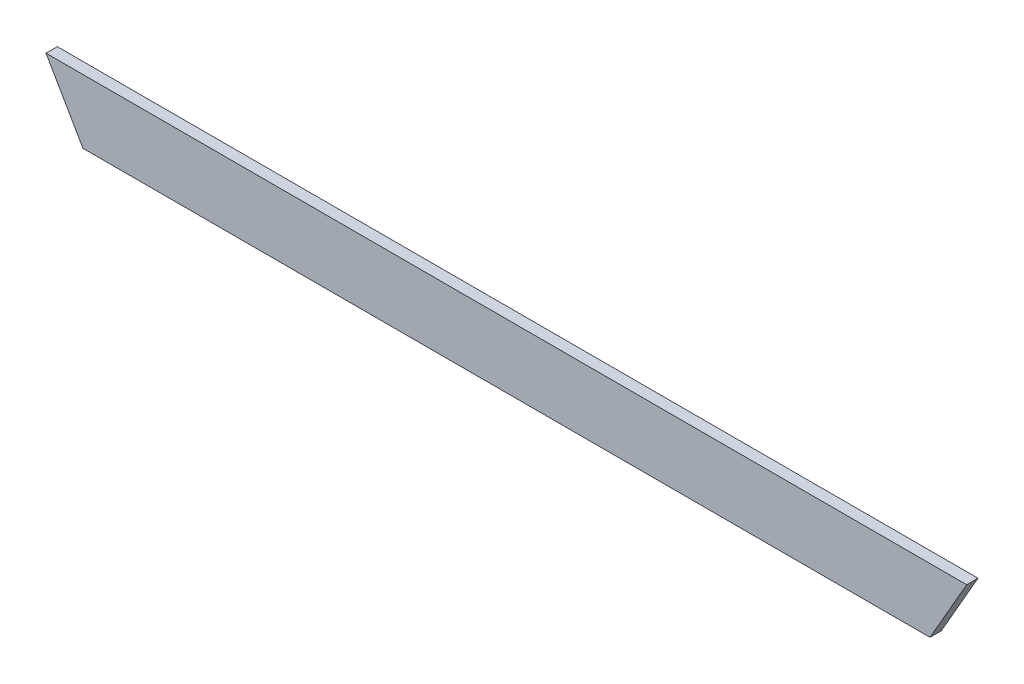
SolidWorks part; units mm, degrees
ref_plane "Front Plane" through (0, 0, 0) normal (0, 0, 1) x (1, 0, 0)
ref_plane "Top Plane" through (0, 0, 0) normal (0, 1, 0) x (1, 0, 0)
ref_plane "Right Plane" through (0, 0, 0) normal (1, 0, 0) x (0, 0, -1)
sketch "Sketch1" plane through (0, 0, 0) normal (0, 0, 1) x (1, 0, 0)
  line L0 (-660.185, 130.6221) -> (-650.3606, 113.6234)
  line L3 (-660.185, 130.6221) -> (-415.373, 130.6221)
  line L4 (-415.373, 130.6221) -> (-425.1396, 113.6234)
  line L5 (-425.1396, 113.6234) -> (-650.3606, 113.6234)
extrude "Boss-Extrude1" add sketch "Sketch1" along normal blind 3
